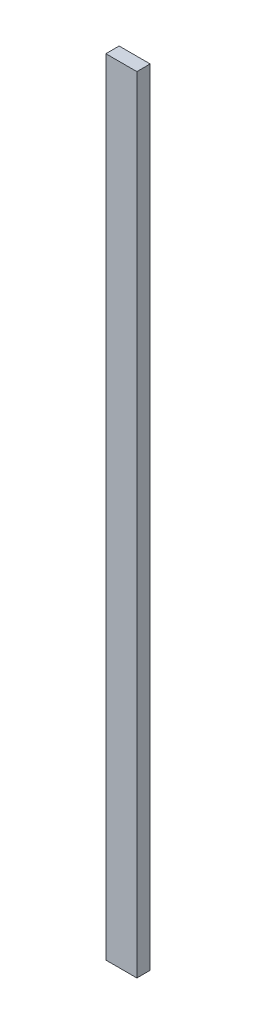
SolidWorks part; units mm, degrees
material "Oak"
ref_plane "Front Plane" through (0, 0, 0) normal (0, 0, 1) x (1, 0, 0)
ref_plane "Top Plane" through (0, 0, 0) normal (0, 1, 0) x (1, 0, 0)
ref_plane "Right Plane" through (0, 0, 0) normal (1, 0, 0) x (0, 0, -1)
sketch "Sketch1" plane through (0, 0, 0) normal (0, 1, 0) x (1, 0, 0)
  line L1 (-44.45, -19.05) -> (44.45, -19.05)
  line L2 (-44.45, -19.05) -> (-44.45, 19.05)
  line L3 (-44.45, 19.05) -> (44.45, 19.05)
  line L4 (44.45, -19.05) -> (44.45, 19.05)
  line L5 (-44.45, -19.05) -> (44.45, 19.05) construction
  line L6 (-44.45, 19.05) -> (44.45, -19.05) construction
  point P0 (0, 0)
  dimension "D1" = 38.1
  dimension "D2" = 88.9
extrude "Boss-Extrude1" add sketch "Sketch1" along normal blind 2247.9 contours L3 L4 L1 L2
